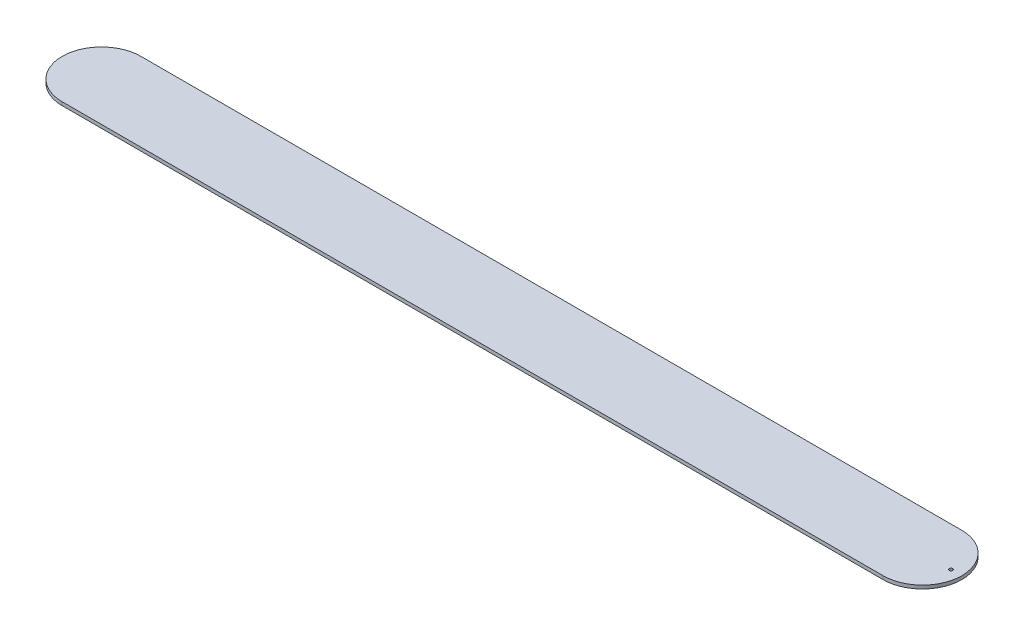
SolidWorks part; units mm, degrees
material "PMMA"
ref_plane "Front Plane" through (0, 0, 0) normal (0, 0, 1) x (1, 0, 0)
ref_plane "Top Plane" through (0, 0, 0) normal (0, 1, 0) x (1, 0, 0)
ref_plane "Right Plane" through (0, 0, 0) normal (1, 0, 0) x (0, 0, -1)
sketch "Sketch1" plane through (0, 0, 0) normal (0, 1, 0) x (-1, 0, 0)
  line L0 (-360, -34.5) -> (360, -34.5)
  line L1 (360, 34.5) -> (-360, 34.5)
  arc A0 (360, -34.5) -> (360, 34.5) centre (360, 0) ccw
  arc A1 (-360, 34.5) -> (-360, -34.5) centre (-360, 0) ccw
extrude "Boss-Extrude1" add sketch "Sketch1" along normal blind 3
hole_wizard "Ø3.0mm Dowel Hole1" positions "Sketch3" profile "Sketch2" hole size "Ø3.0" standard "DIN" end condition through all
sketch "Sketch3" plane through (0, 3, 0) normal (0, 1, 0) x (1, 0, 0)
  line L0 (360, 22) -> (360, -22) construction
  point P0 (385, 0)
  dimension "D1" = 25
sketch "Sketch2" plane through (385, 3, 0) normal (1, 0, 0) x (0, 0, 1)
  line L0 (0, 0) -> (0, 3)
  line L1 (0, 3) -> (1.5, 3)
  line L2 (1.5, 3) -> (1.5, 0)
  line L5 (1.5, 0) -> (0, 0)
  line L11 (0, -6.35) -> (0, 107.95) construction
  dimension "Thru Hole Dia." = 3
  dimension "Thru Hole Depth" = 3
